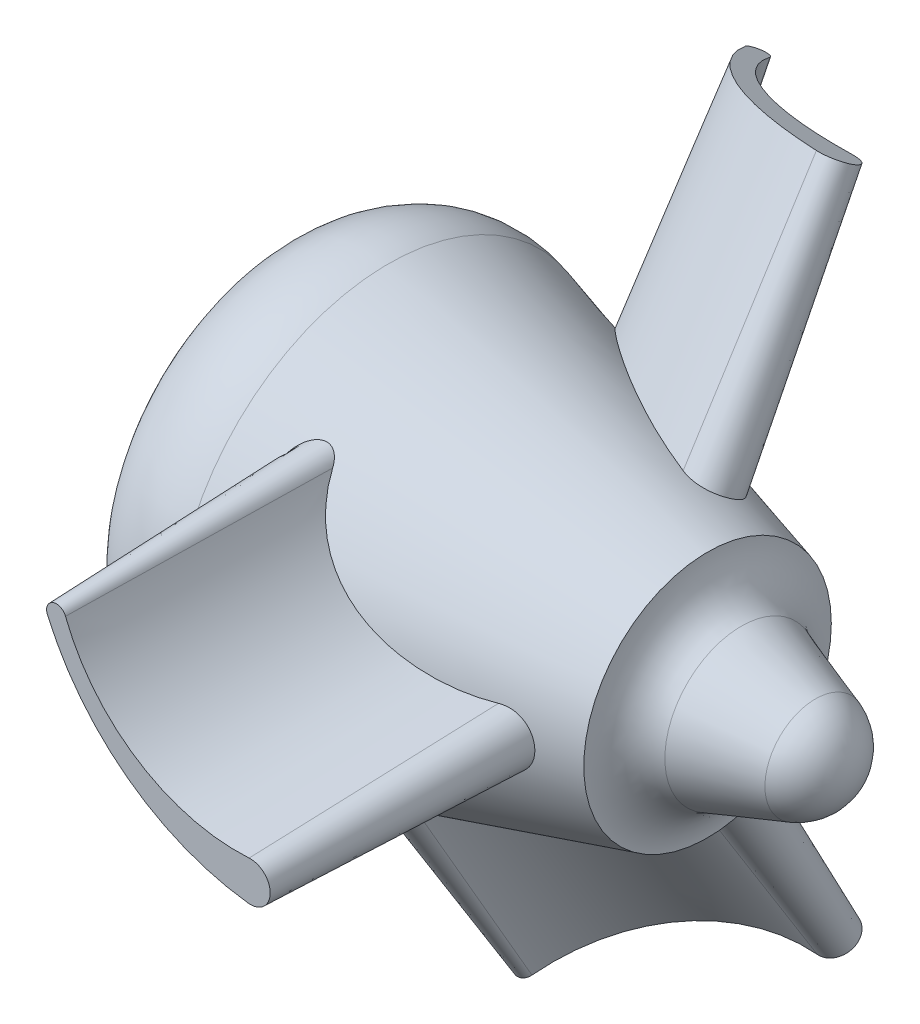
SolidWorks part; units mm, degrees
ref_plane "Alzado" through (0, 0, 0) normal (0, 0, 1) x (1, 0, 0)
ref_plane "Planta" through (0, 0, 0) normal (0, 1, 0) x (1, 0, 0)
ref_plane "Vista lateral" through (0, 0, 0) normal (1, 0, 0) x (0, 0, -1)
sketch "Croquis1" plane through (0, 0, 0) normal (0, 0, 1) x (1, 0, 0)
  line L0 (0, 111) -> (0, 0)
  line L1 (0, 0) -> (522, 0)
  line L2 (106.835, 191.8367) -> (393, 111)
  line L3 (423.2091, 68.5002) -> (489.777, 45.3331)
  arc A0 (106.835, 191.8367) -> (0, 111) centre (84, 111) ccw
  arc A1 (393, 111) -> (423.2091, 68.5002) centre (438, 111) ccw
  arc A2 (522, 0) -> (489.777, 45.3331) centre (474, 0) ccw
  dimension "D1" = 111
  dimension "D3" = 96
  dimension "D4" = 90
  dimension "D5" = 168
  dimension "D2" = 522
  dimension "D6" = 438
  dimension "D7" = 111
revolve "Revolución1" add sketch "Croquis1" angle 360 about L1
sketch "Croquis3" plane through (0, 0, 0) normal (0, 0, 1) x (1, 0, 0)
  arc A0 (139.718, 111.6812) -> (329.474, -29.7921) centre (357.3295, 205.5653) ccw
  arc A1 (178.5926, 127.5586) -> (331.0882, 29.939) centre (321.3383, 182.6281) ccw
  arc A2 (178.5926, 127.5586) -> (139.718, 111.6812) centre (159, 120) ccw
  arc A3 (329.474, -29.7921) -> (331.0882, 29.939) centre (333, 0) ccw
  dimension "D1" = 42
  dimension "D2" = 60
  dimension "D3" = 474
  dimension "D4" = 306
  dimension "D5" = 120
  dimension "D6" = 333
  dimension "D7" = 174
extrude "Boss-Extrude6" add sketch "Croquis3" along normal blind 350 draft 2
pattern_circular "CirPattern1" count 3 every 120 about axis through (0, 0, 0) along (1, 0, 0) of "Boss-Extrude6"
